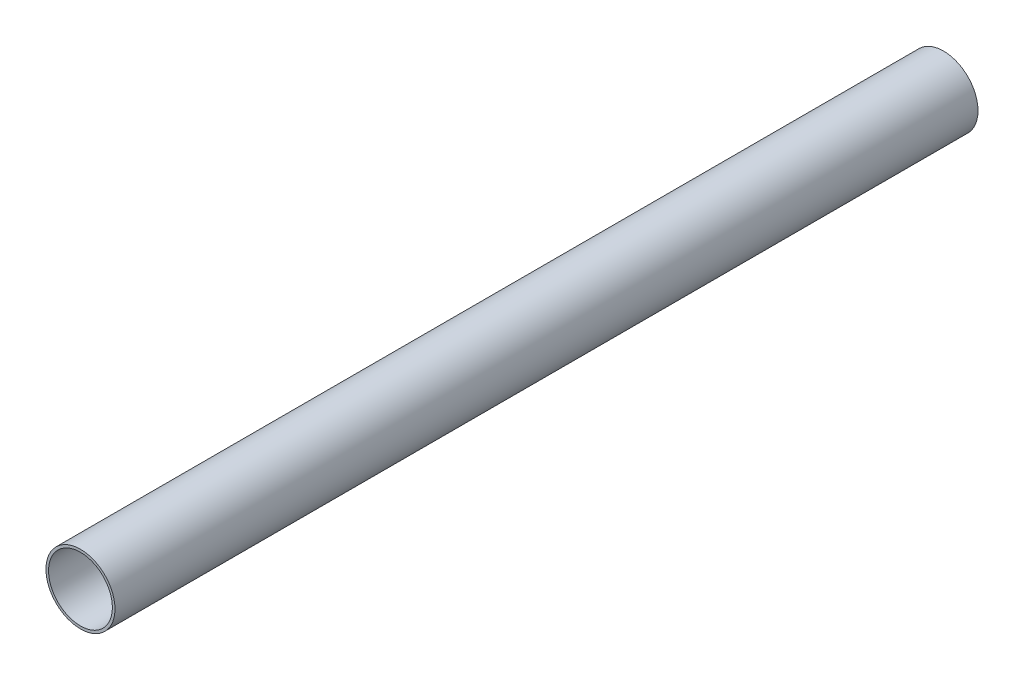
SolidWorks part; units mm, degrees
ref_plane "정면" through (0, 0, 0) normal (0, 0, 1) x (1, 0, 0)
ref_plane "윗면" through (0, 0, 0) normal (0, 1, 0) x (1, 0, 0)
ref_plane "우측면" through (0, 0, 0) normal (1, 0, 0) x (0, 0, -1)
sketch "스케치1" plane through (0, 0, 0) normal (0, 0, 1) x (1, 0, 0)
  circle A0 centre (0, 0) radius 20
  circle A1 centre (0, 0) radius 18.5
  dimension "D1" = 40
  dimension "D2" = 37
extrude "보스-돌출1" add sketch "스케치1" along normal blind 500
